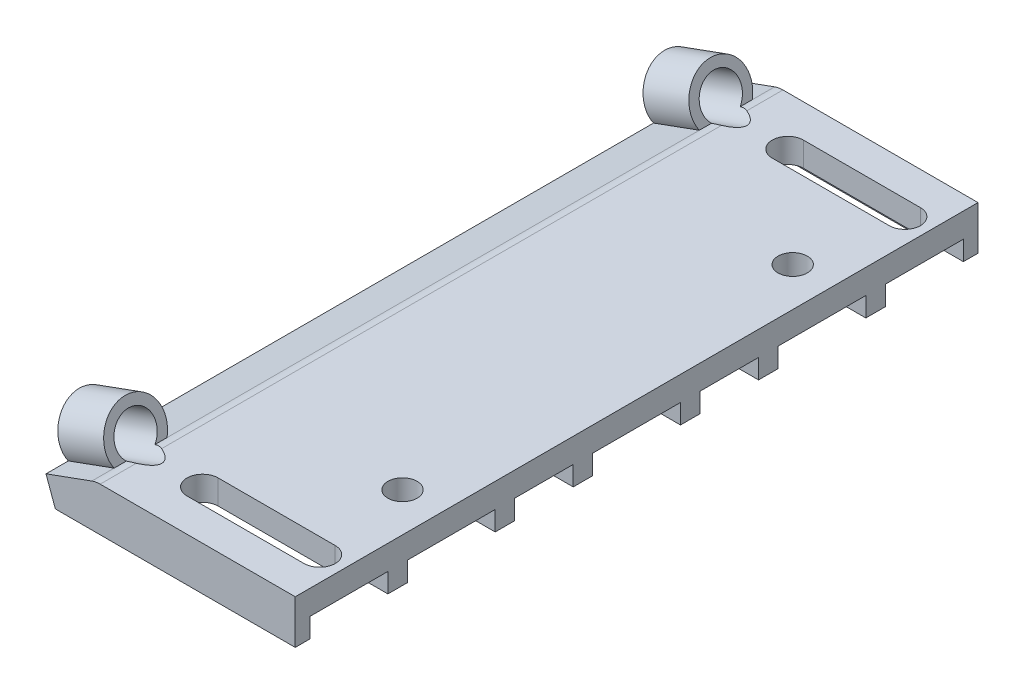
SolidWorks part; units mm, degrees
ref_plane "前视基准面" through (0, 0, 0) normal (0, 0, 1) x (1, 0, 0)
ref_plane "上视基准面" through (0, 0, 0) normal (0, 1, 0) x (1, 0, 0)
ref_plane "右视基准面" through (0, 0, 0) normal (1, 0, 0) x (0, 0, -1)
sketch "草图1" plane through (0, 0, 0) normal (0, 1, 0) x (1, 0, 0)
  line L0 (0, 35) -> (0, -35) construction
  line L1 (-4, 35) -> (4, 35)
  line L2 (-4, 35) -> (-4, -35)
  line L3 (-4, -35) -> (4, -35)
  line L4 (4, 35) -> (4, -35)
  line L5 (-4, 35) -> (4, -35) construction
  line L6 (-4, -35) -> (4, 35) construction
  circle A0 centre (0, 30) radius 1.5
  circle A1 centre (0, 20) radius 1.5
  circle A2 centre (0, -20) radius 1.5
  circle A3 centre (0, -30) radius 1.5
  point P0 (0, 0)
  dimension "D3" = 3
  dimension "D4" = 3
  dimension "D5" = 3
  dimension "D6" = 3
  dimension "D1" = 70
  dimension "D2" = 8
  dimension "D7" = 10
  dimension "D8" = 10
  dimension "D9" = 20
  dimension "D10" = 20
extrude "凸台-拉伸1" add sketch "草图1" along normal blind 2.5
sketch "草图4" plane through (-4, 0, 0) normal (-1, 0, 0) x (0, 0, 1)
  line L1 (-35, 2.5) -> (35, 2.5)
  line L2 (-35, 2.5) -> (-35, 0)
  line L3 (-35, 0) -> (35, 0)
  line L4 (35, 2.5) -> (35, 0)
extrude "凸台-拉伸3" add sketch "草图4" along normal blind 12
sketch "草图6" plane through (0, 0, 35) normal (0, 0, 1) x (1, 0, 0)
  line L0 (-16.8551, 2.3492) -> (-16, 0)
  line L1 (-16, 0) -> (4, 0) construction
  line L2 (-16, 2.5) -> (-16, 0)
  arc A0 (-16, 2.5) -> (-16.8551, 2.3492) centre (-16, 0) ccw
  dimension "D1" = 250
extrude "凸台-拉伸4" add sketch "草图6" against normal up to surface (70 mm away) contours L0 L2 A0 up to face at (-6, 1.25, -35)
sketch "草图7" plane through (-14.1284, -5.1423, 0) normal (-0.9397, -0.342, 0) x (0, 0, 1)
  line L0 (0, 7.9723) -> (0, 5.4723) construction
  line L3 (-35, 7.9723) -> (35, 7.9723) construction
  line L4 (-35, 5.4723) -> (35, 5.4723) construction
  circle A0 centre (30, 9.4723) radius 2.1
  circle A1 centre (-30, 9.4723) radius 2.1
  dimension "D1" = 4.2
  dimension "D2" = 4.2
  dimension "D3" = 30
  dimension "D4" = 30
  dimension "D5" = 1.5
  dimension "D6" = 1.5
extrude "拉伸-薄壁2" add sketch "草图7" along normal blind 5 thin contours A1 | A0
sketch "草图8" plane through (-14.1284, -5.1423, 0) normal (-0.9397, -0.342, 0) x (0, 0, 1)
  line L1 (-35, 7.9723) -> (35, 7.9723)
  line L2 (-35, 7.9723) -> (-35, 5.4723)
  line L3 (-35, 5.4723) -> (35, 5.4723)
  line L4 (35, 7.9723) -> (35, 5.4723)
extrude "凸台-拉伸5" add sketch "草图8" along normal up to surface (5 mm away) up to face at (-22.0665, 2.0487, -26.9)
sketch "草图9" plane through (-18.8268, -6.8524, 0) normal (-0.9397, -0.342, 0) x (0, 0, 1)
  circle A0 centre (-30, 9.4723) radius 2.1
  circle A1 centre (30, 9.4723) radius 2.1
  dimension "D1" = 4.2
  dimension "D2" = 4.2
extrude "切除-拉伸1" cut sketch "草图9" against normal up to next
sketch "草图10" plane through (-14.1284, -5.1423, 0) normal (0.9397, 0.342, 0) x (0, 0, -1)
  circle A0 centre (-30, 9.4723) radius 4.15
  circle A1 centre (30, 9.4723) radius 4.15
  dimension "D1" = 8.3
  dimension "D2" = 8.3
sketch "草图11" plane through (0, 2.5, 0) normal (0, 1, 0) x (1, 0, 0)
  line L0 (0, 30) -> (-15.9487, 30) construction
  line L1 (0, -30) -> (-15.9487, -30) construction
  line L2 (1.5, 30) -> (-10.5, 30) construction
  line L3 (1.5, 28.4) -> (-10.5, 28.4)
  line L4 (1.5, 31.6) -> (-10.5, 31.6)
  line L5 (4, -35) -> (4, 35) construction
  line L6 (4, 0) -> (-16, 0) construction
  line L7 (-16, -28.7019) -> (-16, 28.7019) construction
  line L8 (1.5, -30) -> (-10.5, -30) construction
  line L11 (1.5, -31.6) -> (-10.5, -31.6)
  line L12 (1.5, -28.4) -> (-10.5, -28.4)
  circle A0 centre (0, 30) radius 1.5 construction
  arc A1 (1.5, 28.4) -> (1.5, 31.6) centre (1.5, 30) ccw
  arc A2 (-10.5, 31.6) -> (-10.5, 28.4) centre (-10.5, 30) ccw
  arc A5 (1.5, -31.6) -> (1.5, -28.4) centre (1.5, -30) ccw
  arc A6 (-10.5, -28.4) -> (-10.5, -31.6) centre (-10.5, -30) ccw
  ellipse E0 centre (-17.3681, 30) end of major axis (-17.3681, 34.15) minor radius 1.4194 construction
  ellipse E1 centre (-17.3681, -30) end of major axis (-17.3681, -34.15) minor radius 1.4194 construction
  point P22 (-4.5, 30)
  point P35 (-4.5, -30)
  dimension "D2" = 1.6
  dimension "D5" = 1.6
  dimension "D1" = 12
  dimension "D3" = 8.5
  dimension "D4" = 8.5
  dimension "D6" = 12
extrude "切除-拉伸2" cut sketch "草图11" against normal blind 10
sketch "草图13" plane through (4, 0, 0) normal (1, 0, 0) x (0, 0, -1)
  line L0 (-35, 0) -> (35, 0)
  line L1 (-35, 0) -> (-35, -2)
  line L2 (35, 0) -> (35, -2)
  line L3 (-35, -2) -> (35, -2)
  dimension "D1" = 2
sketch "草图15" plane through (4, 0, 0) normal (1, 0, 0) x (0, 0, -1)
  line L0 (-35, -2) -> (35, -2) construction
  line L1 (-35, 0) -> (-33.5, 0)
  line L2 (-35, 0) -> (-35, -2)
  line L3 (-35, -2) -> (-33.5, -2)
  line L4 (-33.5, 0) -> (-33.5, -2)
  line L5 (-35, 0) -> (35, 0) construction
  line L6 (-25.5, 0) -> (-23.5, 0)
  line L7 (-25.5, 0) -> (-25.5, -2)
  line L8 (-25.5, -2) -> (-23.5, -2)
  line L9 (-23.5, 0) -> (-23.5, -2)
  line L11 (-14.5, 0) -> (-12.5, 0)
  line L12 (-14.5, 0) -> (-14.5, -2)
  line L13 (-14.5, -2) -> (-12.5, -2)
  line L14 (-12.5, 0) -> (-12.5, -2)
  line L15 (-6.5, 0) -> (-4.5, 0)
  line L16 (-6.5, 0) -> (-6.5, -2)
  line L17 (-6.5, -2) -> (-4.5, -2)
  line L18 (-4.5, 0) -> (-4.5, -2)
  line L19 (4.5, 0) -> (6.5, 0)
  line L20 (4.5, 0) -> (4.5, -2)
  line L21 (4.5, -2) -> (6.5, -2)
  line L22 (6.5, 0) -> (6.5, -2)
  line L23 (12.5, 0) -> (14.5, 0)
  line L24 (12.5, 0) -> (12.5, -2)
  line L25 (12.5, -2) -> (14.5, -2)
  line L26 (14.5, 0) -> (14.5, -2)
  line L31 (35, -2) -> (33.5, -2)
  line L32 (35, -2) -> (35, 0)
  line L33 (35, 0) -> (33.5, 0)
  line L34 (33.5, -2) -> (33.5, 0)
  line L35 (23.5, -2) -> (25.5, -2)
  line L36 (23.5, -2) -> (23.5, 0)
  line L37 (23.5, 0) -> (25.5, 0)
  line L38 (25.5, -2) -> (25.5, 0)
  dimension "D1" = 1.5
  dimension "D2" = 8
  dimension "D3" = 2
  dimension "D4" = 9
  dimension "D5" = 2
  dimension "D6" = 2
  dimension "D7" = 6
  dimension "D8" = 1.5
  dimension "D9" = 2
  dimension "D10" = 8
  dimension "D11" = 9
  dimension "D12" = 2
  dimension "D13" = 2
  dimension "D14" = 6
extrude "凸台-拉伸6" add sketch "草图15" against normal up to surface (25.3209 mm away)
